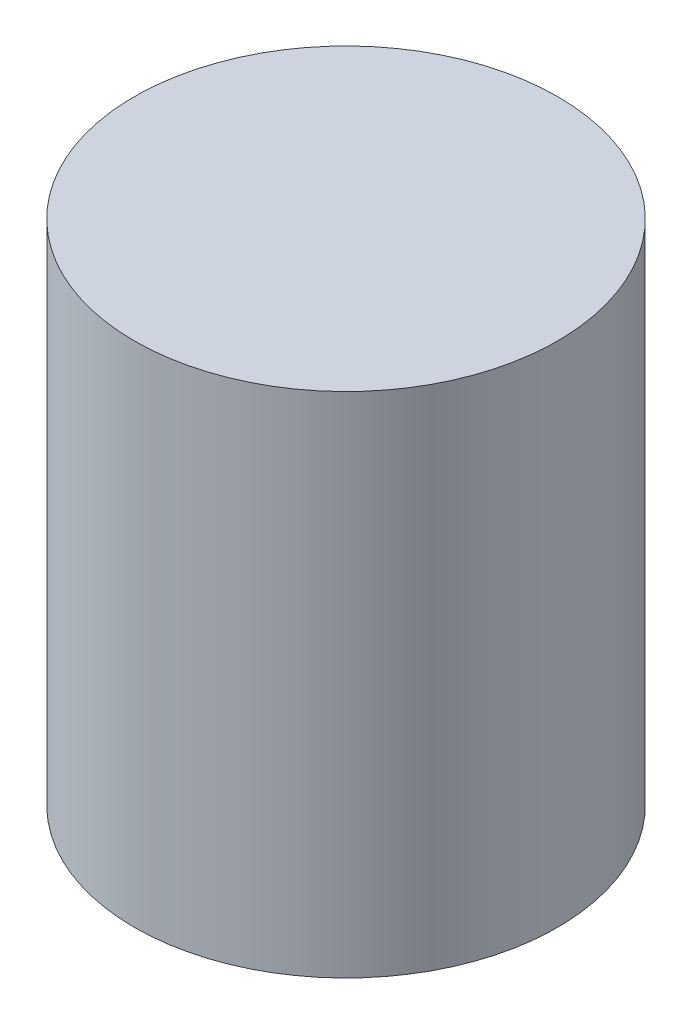
SolidWorks part; units mm, degrees
ref_plane "Front Plane" through (0, 0, 0) normal (0, 0, 1) x (1, 0, 0)
ref_plane "Top Plane" through (0, 0, 0) normal (0, 1, 0) x (1, 0, 0)
ref_plane "Right Plane" through (0, 0, 0) normal (1, 0, 0) x (0, 0, -1)
sketch "Sketch1" plane through (0, 0, 0) normal (0, 1, 0) x (1, 0, 0)
  circle A0 centre (0, 0) radius 0.635
  dimension "D1" = 1.27
extrude "Boss-Extrude1" add sketch "Sketch1" along normal blind 1.524
